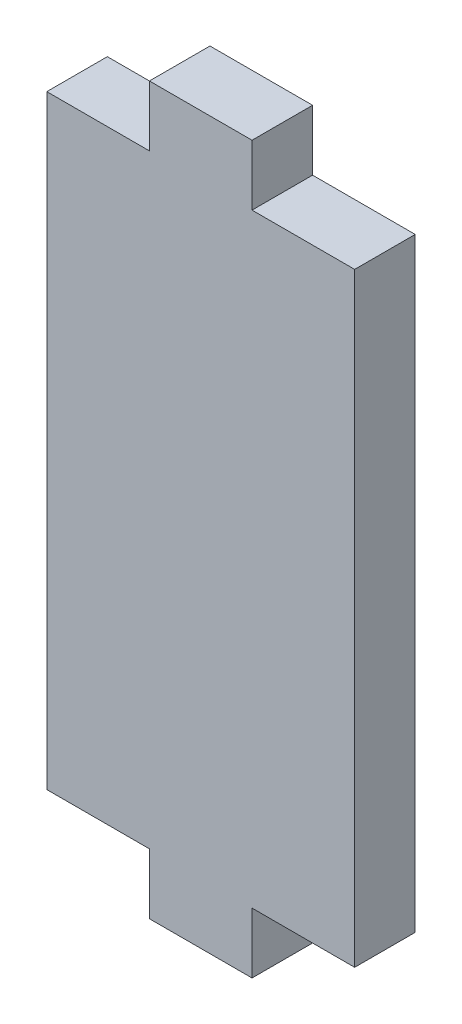
SolidWorks part; units mm, degrees
ref_plane "Front Plane" through (0, 0, 0) normal (0, 0, 1) x (1, 0, 0)
ref_plane "Top Plane" through (0, 0, 0) normal (0, 1, 0) x (1, 0, 0)
ref_plane "Right Plane" through (0, 0, 0) normal (1, 0, 0) x (0, 0, -1)
sketch "Sketch1" plane through (0, 0, 0) normal (0, 0, 1) x (1, 0, 0)
  line L1 (-15, -29.45) -> (15, -29.45)
  line L2 (-15, -29.45) -> (-15, 29.45)
  line L3 (-15, 29.45) -> (15, 29.45)
  line L4 (15, -29.45) -> (15, 29.45)
  line L5 (-15, -29.45) -> (15, 29.45) construction
  line L6 (-15, 29.45) -> (15, -29.45) construction
  line L7 (-5, 23.55) -> (5, 23.55)
  line L8 (-5, 23.55) -> (-5, 35.35)
  line L9 (-5, 35.35) -> (5, 35.35)
  line L10 (5, 23.55) -> (5, 35.35)
  line L11 (-5, 23.55) -> (5, 35.35) construction
  line L12 (-5, 35.35) -> (5, 23.55) construction
  line L13 (-5, -23.55) -> (5, -23.55)
  line L14 (-5, -23.55) -> (-5, -35.35)
  line L15 (-5, -35.35) -> (5, -35.35)
  line L16 (5, -23.55) -> (5, -35.35)
  line L17 (-5, -23.55) -> (5, -35.35) construction
  line L18 (-5, -35.35) -> (5, -23.55) construction
  point P0 (0, 0)
  point P5 (0, 29.45)
  point P11 (0, -29.45)
  dimension "D1" = 58.9
  dimension "D2" = 30
  dimension "D3" = 11.8
  dimension "D4" = 10
extrude "Boss-Extrude1" add sketch "Sketch1" along normal blind 5.9 contours L3 L10 L9 L8 | L7 L10 L3 L8 | L13 L16 L1 L4 L3 L10 L7 L8 L2 L14 | L16 L13 L14 L1 | L16 L1 L14 L15
equation "\"e\" = 5.9"
equation "\"D1@Boss-Extrude1\"=\"e\""
equation "\"D3@Sketch1\"= 2 * \"e\""
equation "\"D1@Sketch1\"= 38.45 + 8.65 + 2 * \"e\""
